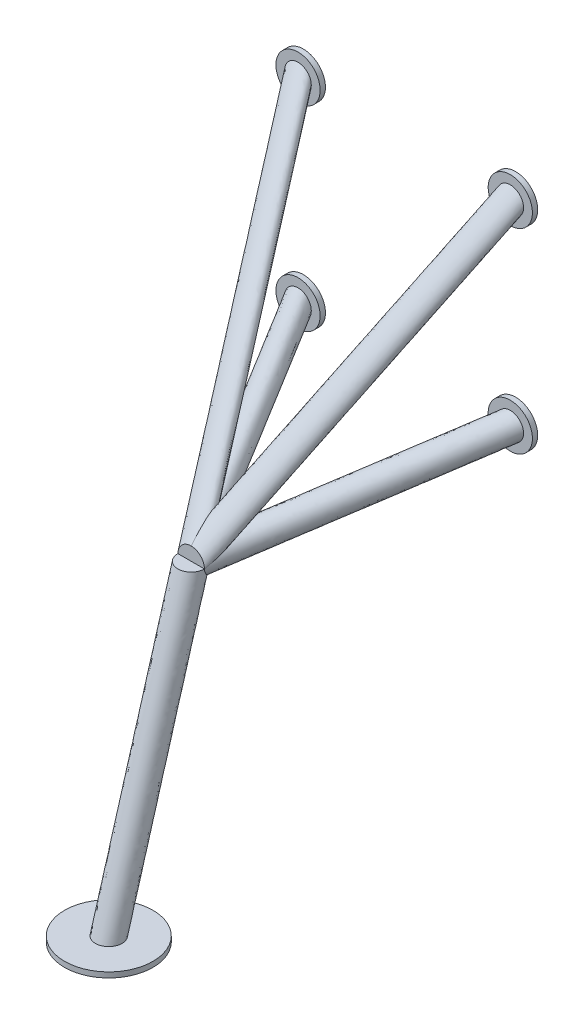
SolidWorks part; units mm, degrees
material "Pure Gold"
ref_plane "Front Plane" through (0, 0, 0) normal (0, 0, 1) x (1, 0, 0)
ref_plane "Top Plane" through (0, 0, 0) normal (0, 1, 0) x (1, 0, 0)
ref_plane "Right Plane" through (0, 0, 0) normal (1, 0, 0) x (0, 0, -1)
sketch "Sketch2" plane through (0, 0, 0) normal (0, 1, 0) x (1, 0, 0)
  circle A0 centre (191.8349, -431.8) radius 63.5
  dimension "D1" = 127
  dimension "D2" = 431.8
extrude "Boss-Extrude2" add sketch "Sketch2" along normal blind 7.62 from offset 444.5 separate body offset against normal yes
ref_point "Point1"
ref_plane "Plane1" through (191.8349, 0, 0) normal (1, 0, 0) x (0, 0, -1)
sketch "Sketch3" plane through (191.8349, 0, 0) normal (1, 0, 0) x (0, 0, -1)
  line L0 (-431.8, -436.88) -> (-313.4927, -30.2805)
sketch "Sketch1" plane through (0, 0, 0) normal (0, 0, 1) x (1, 0, 0)
  circle A0 centre (39.4349, 61.582) radius 31.75
  circle A1 centre (39.4349, 342.1224) radius 31.75
  circle A2 centre (344.2349, 342.1224) radius 31.75
  circle A3 centre (344.2349, 61.582) radius 31.75
  dimension "D3" = 63.5
  dimension "D2" = 304.8
extrude "Boss-Extrude1" add sketch "Sketch1" along normal blind 7.62
sketch "Sketch4" plane through (0, -436.88, 0) normal (0, 1, 0) x (1, 0, 0)
  circle A0 centre (191.8349, -431.8) radius 19.05
  dimension "D1" = 38.1
sweep "Sweep1" add profiles "Sketch4" path "Sketch3"
ref_point "Point2"
ref_point "Point3"
ref_point "Point4"
sketch3d "3DSketch2"
  line L0 (39.4349, 342.1224, 7.62) -> (191.8349, -30.2805, 313.4927)
sketch "Sketch6" plane through (0, 0, 7.62) normal (0, 0, 1) x (1, 0, 0)
  circle A0 centre (39.4349, 342.1224) radius 19.05
  dimension "D1" = 38.1
sweep "Sweep2" add profiles "Sketch6" path "3DSketch2"
sketch3d "3DSketch3"
  line L0 (39.4349, 61.582, 7.62) -> (191.8349, -30.2805, 313.4927)
sketch "Sketch7" plane through (0, 0, 7.62) normal (0, 0, 1) x (1, 0, 0)
  circle A0 centre (39.4349, 61.582) radius 19.05
  dimension "D1" = 38.1
sweep "Sweep3" add profiles "Sketch7" path "3DSketch3"
mirror "Mirror1" about plane through (191.8349, 0, 0) normal (1, 0, 0) of "Sweep2", "Sweep3"
